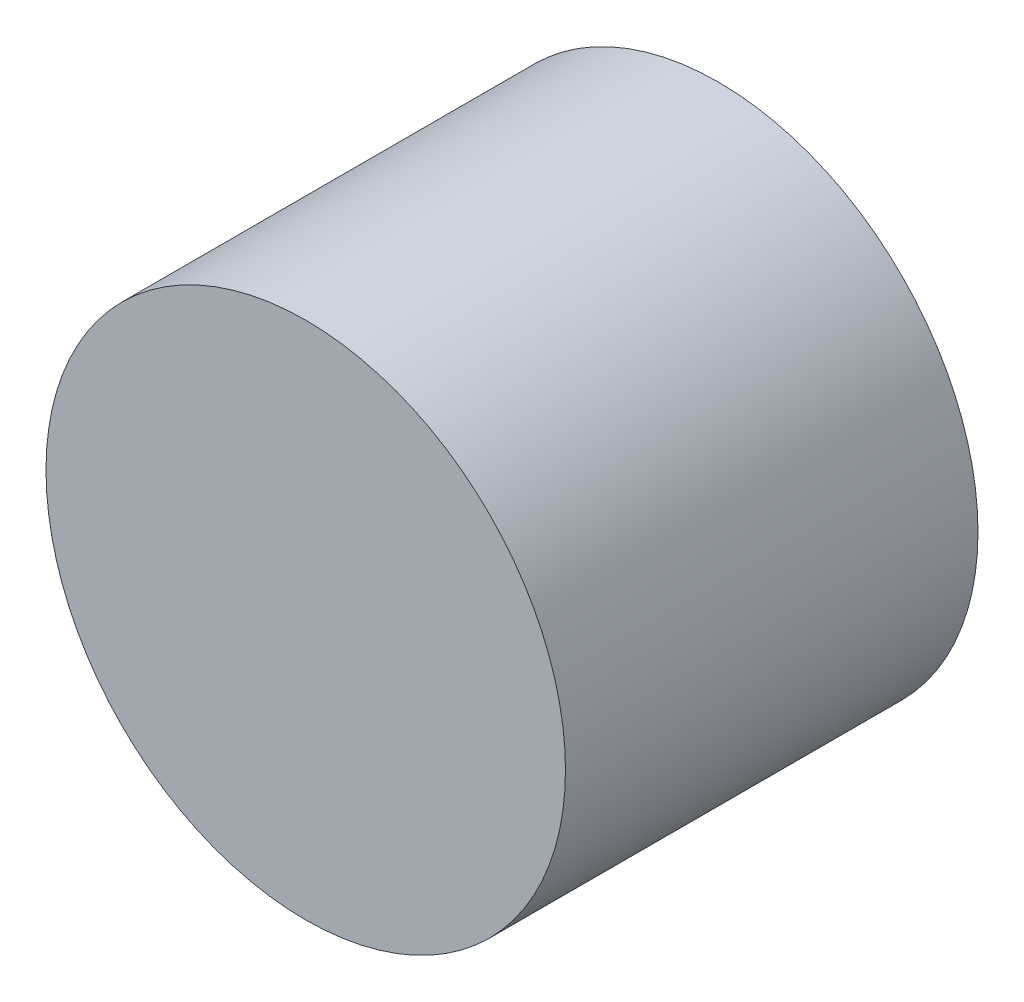
SolidWorks part; units mm, degrees
ref_plane "Front" through (0, 0, 0) normal (0, 0, 1) x (1, 0, 0)
ref_plane "Top" through (0, 0, 0) normal (0, 1, 0) x (1, 0, 0)
ref_plane "Right" through (0, 0, 0) normal (1, 0, 0) x (0, 0, -1)
sketch "Sketch1" plane through (0, 0, 0) normal (0, 0, 1) x (1, 0, 0)
  circle A0 centre (0, 0) radius 8.5
  dimension "D1" = 17
extrude "Boss-Extrude1" add sketch "Sketch1" along normal blind 13.5
